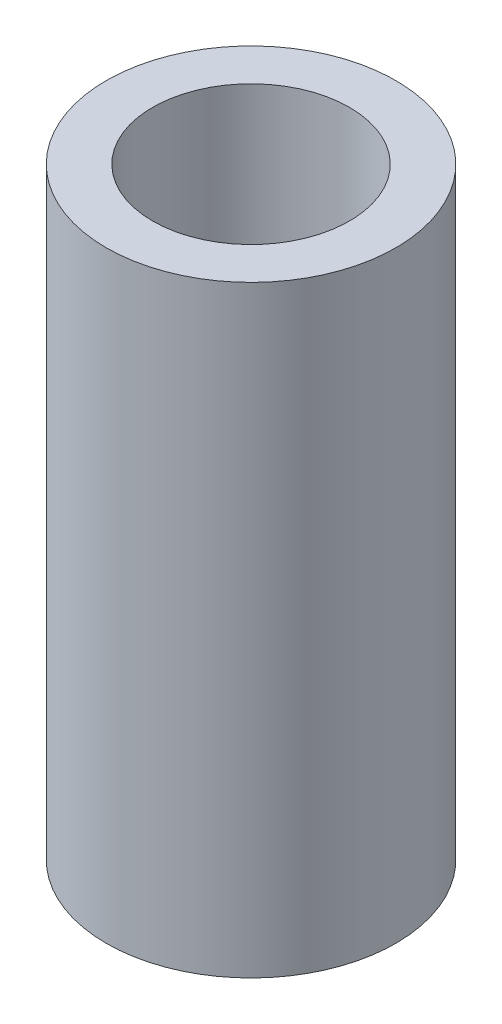
SolidWorks part; units mm, degrees
material "6063-T6"
ref_plane "Front Plane" through (0, 0, 0) normal (0, 0, 1) x (1, 0, 0)
ref_plane "Top Plane" through (0, 0, 0) normal (0, 1, 0) x (1, 0, 0)
ref_plane "Right Plane" through (0, 0, 0) normal (1, 0, 0) x (0, 0, -1)
sketch "Sketch1" plane through (0, 0, 0) normal (0, 1, 0) x (1, 0, 0)
  circle A0 centre (0, 0) radius 12.5
  circle A1 centre (0, 0) radius 8.5
  dimension "D1" = 25
  dimension "D2" = 17
extrude "Boss-Extrude1" add sketch "Sketch1" along normal blind 52
